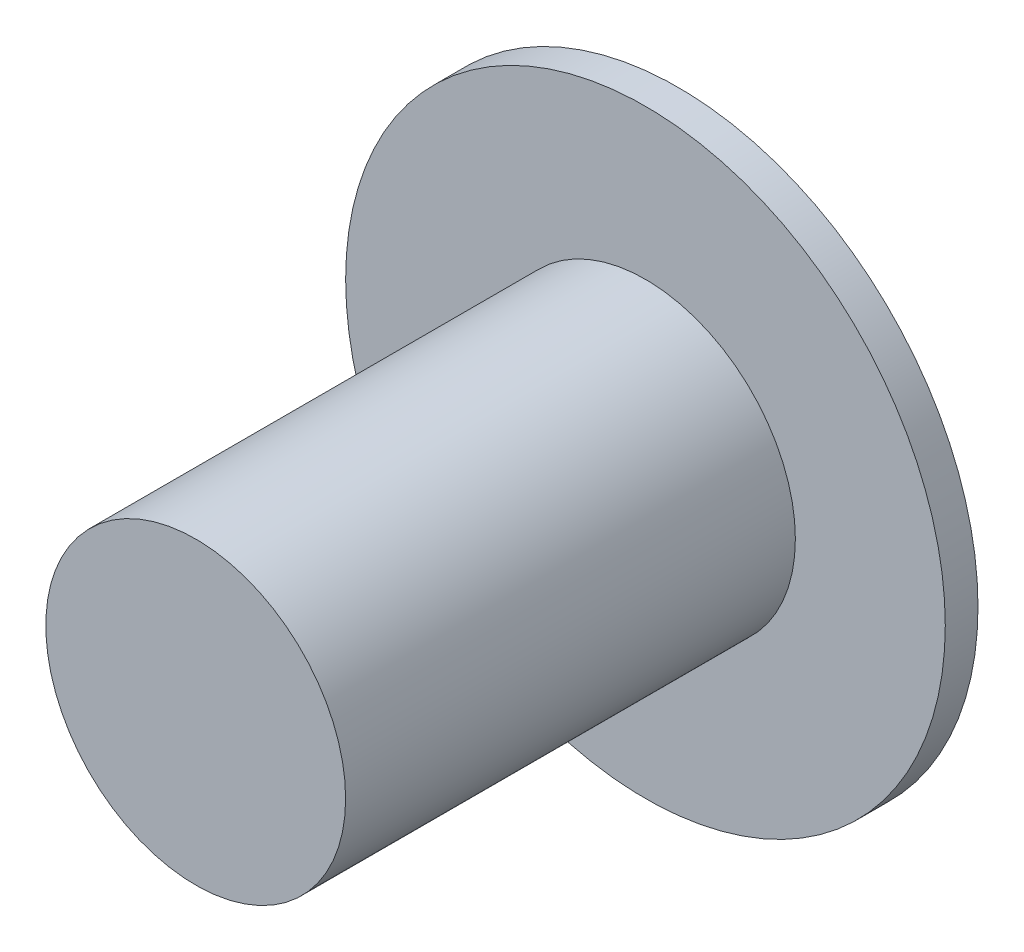
SolidWorks part; units mm, degrees
ref_plane "Front Plane" through (0, 0, 0) normal (0, 0, 1) x (1, 0, 0)
ref_plane "Top Plane" through (0, 0, 0) normal (0, 1, 0) x (1, 0, 0)
ref_plane "Right Plane" through (0, 0, 0) normal (1, 0, 0) x (0, 0, -1)
sketch "Sketch1" plane through (0, 0, 0) normal (0, 0, 1) x (1, 0, 0)
  circle A0 centre (0, 0) radius 11
  dimension "D1" = 22
extrude "Boss-Extrude2" add sketch "Sketch1" along normal blind 5
sketch "Sketch3" plane through (0, 0, 5) normal (0, 0, 1) x (1, 0, 0)
  circle A0 centre (0, 0) radius 22
  dimension "D1" = 44
extrude "Boss-Extrude3" add sketch "Sketch3" along normal blind 2.4
sketch "Sketch4" plane through (0, 0, 7.4) normal (0, 0, 1) x (1, 0, 0)
  circle A0 centre (0, 0) radius 11
  dimension "D1" = 22
extrude "Boss-Extrude4" add sketch "Sketch4" along normal blind 33
